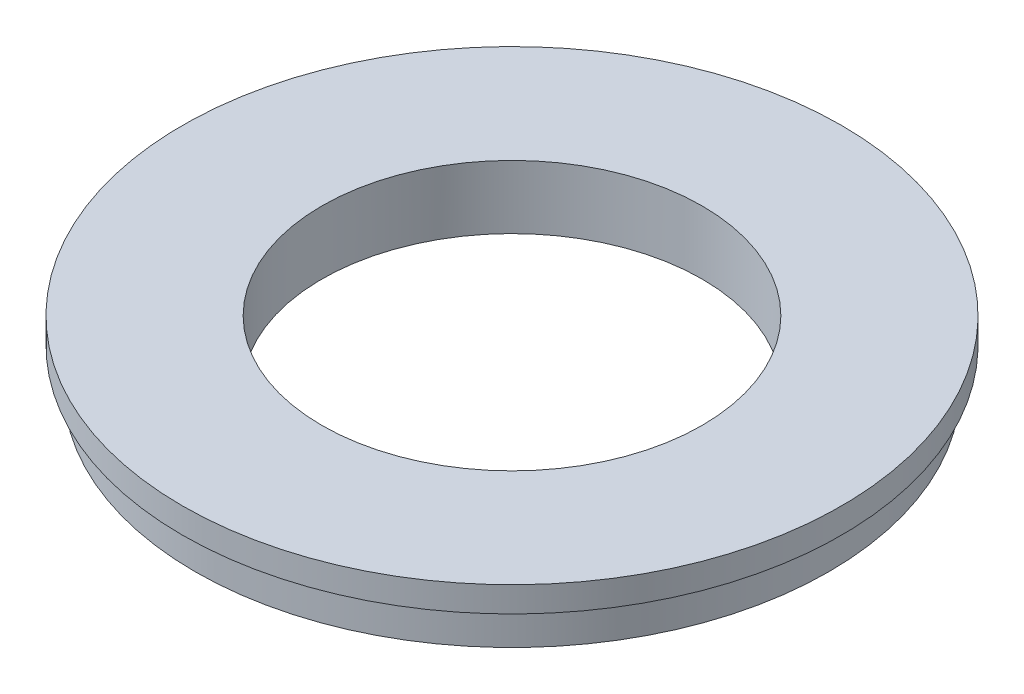
SolidWorks part; units mm, degrees
ref_plane "Front Plane" through (0, 0, 0) normal (0, 0, 1) x (1, 0, 0)
ref_plane "Top Plane" through (0, 0, 0) normal (0, 1, 0) x (1, 0, 0)
ref_plane "Right Plane" through (0, 0, 0) normal (1, 0, 0) x (0, 0, -1)
sketch "Sketch1" plane through (0, 0, 0) normal (0, 1, 0) x (1, 0, 0)
  circle A0 centre (0, 0) radius 26
  circle A1 centre (0, 0) radius 15
  dimension "D1" = 52
  dimension "D2" = 30
extrude "Boss-Extrude1" add sketch "Sketch1" along normal blind 2
sketch "Sketch2" plane through (0, 0, 0) normal (0, -1, 0) x (1, 0, 0)
  circle A3 centre (0, 0) radius 25
  circle A4 centre (0, 0) radius 15 construction
  circle A5 centre (0, 0) radius 15
  dimension "D1" = 50
extrude "Boss-Extrude3" add sketch "Sketch2" along normal blind 3
